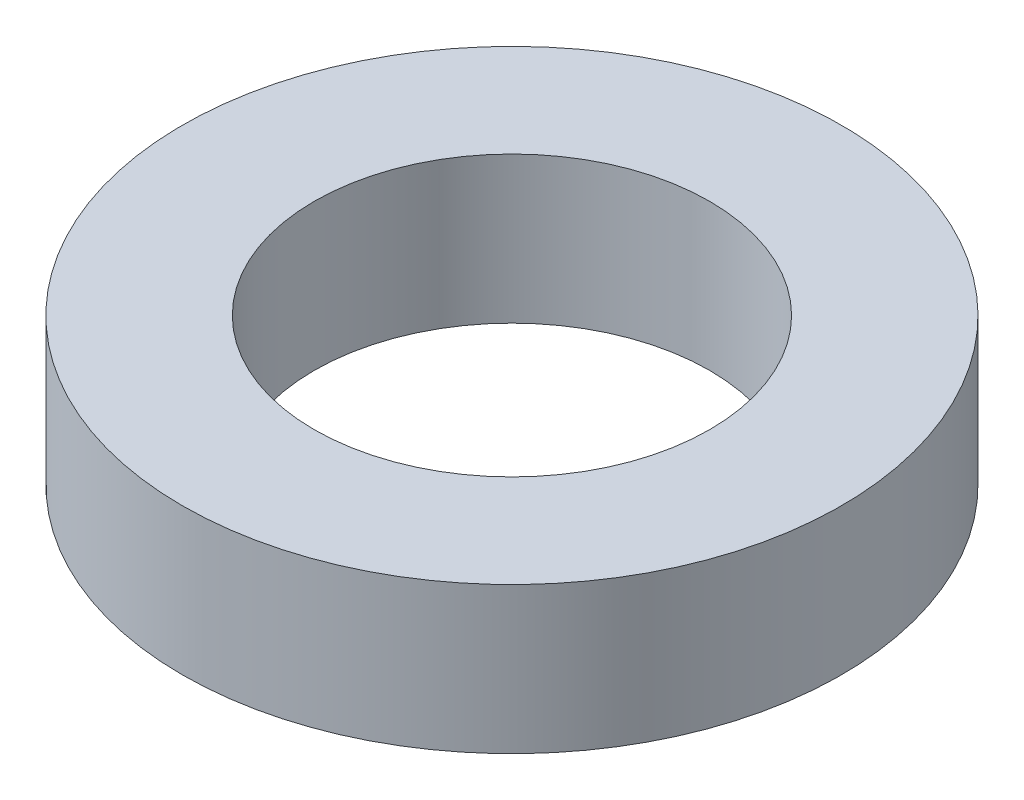
SolidWorks part; units mm, degrees
ref_plane "Front Plane" through (0, 0, 0) normal (0, 0, 1) x (1, 0, 0)
ref_plane "Top Plane" through (0, 0, 0) normal (0, 1, 0) x (1, 0, 0)
ref_plane "Right Plane" through (0, 0, 0) normal (1, 0, 0) x (0, 0, -1)
sketch "Sketch1" plane through (0, 0, 0) normal (0, 1, 0) x (1, 0, 0)
  circle A0 centre (0, 0) radius 2.7
  circle A1 centre (0, 0) radius 4.5
  dimension "D1" = 5.4
  dimension "D2" = 9
extrude "Boss-Extrude1" add sketch "Sketch1" along normal mid plane 2
